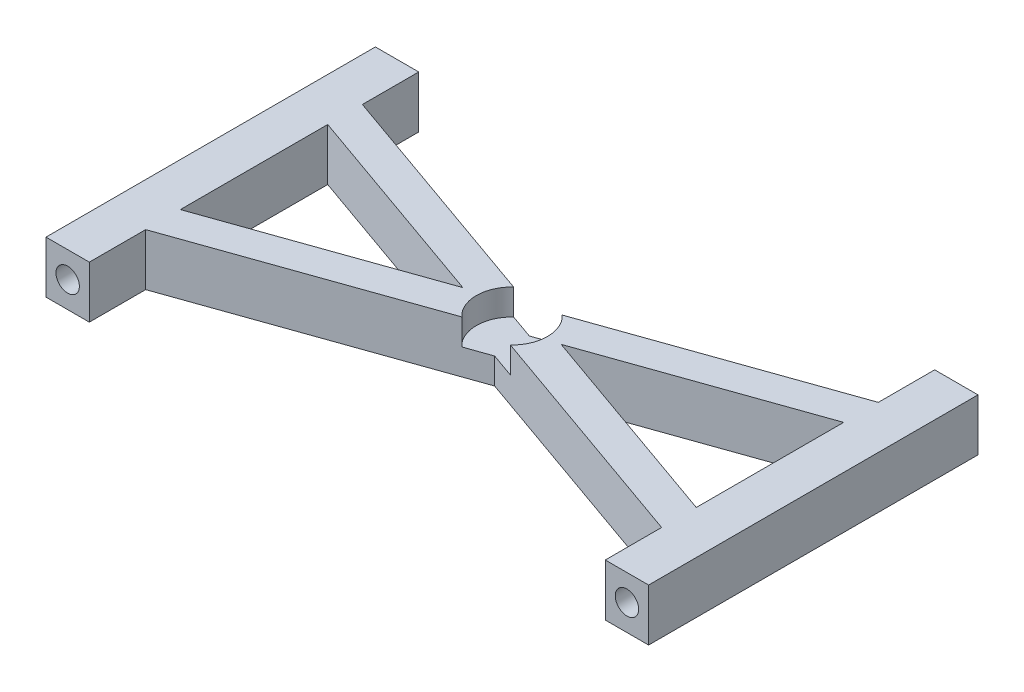
SolidWorks part; units mm, degrees
ref_plane "Front Plane" through (0, 0, 0) normal (0, 0, 1) x (1, 0, 0)
ref_plane "Top Plane" through (0, 0, 0) normal (0, 1, 0) x (1, 0, 0)
ref_plane "Right Plane" through (0, 0, 0) normal (1, 0, 0) x (0, 0, -1)
sketch "Sketch1" plane through (0, 0, 0) normal (0, 1, 0) x (1, 0, 0)
  line L0 (32.26, 0) -> (32.26, 4.019) construction
  line L1 (0, 0) -> (64.52, 0)
  line L2 (0, 0) -> (0, 25)
  line L3 (0, 25) -> (64.52, 25)
  line L4 (64.52, 0) -> (64.52, 25)
  line L5 (-2.5, 31.5) -> (2.5, 31.5)
  line L6 (-2.5, 31.5) -> (-2.5, -6.5)
  line L7 (-2.5, -6.5) -> (2.5, -6.5)
  line L8 (2.5, 31.5) -> (2.5, -6.5)
  line L9 (0, 12.5) -> (7.5775, 12.5) construction
  line L10 (0, 0) -> (0, -8.8754) construction
  line L11 (62.02, 31.5) -> (62.02, -6.5)
  line L12 (67.02, -6.5) -> (62.02, -6.5)
  line L13 (67.02, 31.5) -> (67.02, -6.5)
  line L14 (67.02, 31.5) -> (62.02, 31.5)
  line L15 (2.5, 0) -> (62.02, 21)
  line L16 (62.02, 25) -> (2.5, 4)
  line L17 (2.5, 25) -> (62.02, 4)
  line L18 (62.02, 0) -> (2.5, 21)
  point P11 (0, 12.5)
  point P12 (2.5, 12.5)
  point P13 (0, 31.5)
  point P21 (64.52, 31.5)
  point P22 (62.02, 12.5)
  point P23 (64.52, 12.5)
  dimension "D1" = 64.52
  dimension "D2" = 25
  dimension "D3" = 5
  dimension "D4" = 38
  dimension "D5" = 4
  dimension "D6" = 4
extrude "Boss-Extrude1" add sketch "Sketch1" along normal blind 6 contours L8 L5 L6 L7 L1 L2 L3 | L8 L3 L2 L1 | L18 L16 L17 L8 | L18 L15 L17 L16 | L16 L17 L15 L11 | L15 L18 L16 L8 | L18 L11 L17 L15 | L3 L11 L1 L4 | L13 L14 L11 L3 L4 L1 L12
sketch "Sketch2" plane through (0, 0, -31.5) normal (0, 0, -1) x (-1, 0, 0)
  line L0 (-32.26, 6) -> (-32.26, 0) construction
  line L1 (-32.26, 6) -> (-32.26, 0)
  line L2 (-2.5, 0) -> (2.5, 6) construction
  line L4 (-2.5, 0) -> (2.5, 0)
  line L5 (2.5, 0) -> (2.5, 6)
  line L6 (2.5, 6) -> (-2.5, 6)
  line L7 (-2.5, 6) -> (-2.5, 0)
  line L8 (-2.5, 0) -> (2.5, 0)
  line L9 (2.5, 0) -> (2.5, 6)
  line L11 (-2.5, 6) -> (-2.5, 0)
  line L15 (2.5, 6) -> (-2.5, 6)
  circle A0 centre (0, 3) radius 1.35
  circle A1 centre (-64.52, 3) radius 1.35
  dimension "D2" = 2.7
  dimension "D1" = 0
extrude "Cut-Extrude1" cut sketch "Sketch2" against normal through all contours L2 A0 | A0 L2 | A1
sketch "Esquisse1" plane through (0, 6, 0) normal (0, 1, 0) x (1, 0, 0)
  line L0 (26.5914, 12.5) -> (37.9286, 12.5) construction
  line L1 (32.26, 14.5) -> (32.26, 10.5) construction
  circle A0 centre (32.26, 12.5) radius 4.1
  dimension "D1" = 8.2
extrude "Enlèv. mat.-Extru.1" cut sketch "Esquisse1" against normal blind 3
